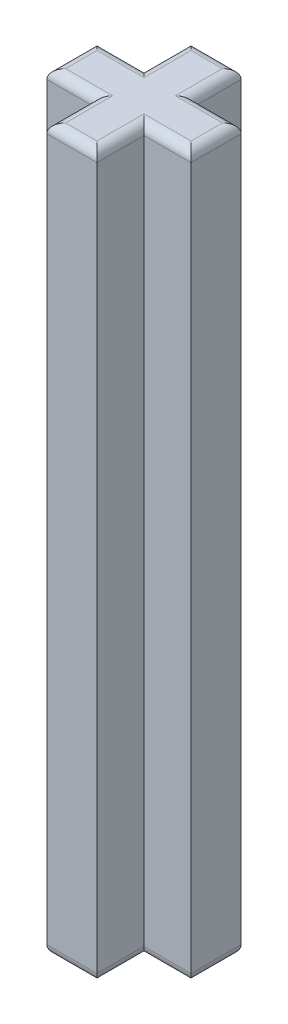
SolidWorks part; units mm, degrees
ref_plane "Front Plane" through (0, 0, 0) normal (0, 0, 1) x (1, 0, 0)
ref_plane "Top Plane" through (0, 0, 0) normal (0, 1, 0) x (1, 0, 0)
ref_plane "Right Plane" through (0, 0, 0) normal (1, 0, 0) x (0, 0, -1)
sketch "Sketch1" plane through (0, 0, 0) normal (0, 1, 0) x (1, 0, 0)
  line L0 (0.8, 0.8) -> (2.3, 0.8)
  line L1 (-2.3, -0.8) -> (-0.8, -0.8)
  line L2 (-2.3, -0.8) -> (-2.3, 0.8)
  line L3 (-2.3, 0.8) -> (-0.8, 0.8)
  line L4 (2.3, -0.8) -> (2.3, 0.8)
  line L5 (-2.3, -0.8) -> (2.3, 0.8) construction
  line L6 (-2.3, 0.8) -> (2.3, -0.8) construction
  line L7 (-0.8, -2.3) -> (0.8, -2.3)
  line L8 (-0.8, -2.3) -> (-0.8, -0.8)
  line L9 (-0.8, 2.3) -> (0.8, 2.3)
  line L10 (0.8, -2.3) -> (0.8, -0.8)
  line L11 (-0.8, -2.3) -> (0.8, 2.3) construction
  line L12 (-0.8, 2.3) -> (0.8, -2.3) construction
  line L13 (0.8, 0.8) -> (0.8, 2.3)
  line L14 (0.8, -0.8) -> (2.3, -0.8)
  line L15 (-0.8, 0.8) -> (-0.8, 2.3)
  point P0 (0, 0)
  point P6 (0, 0)
  dimension "D1" = 1.6
  dimension "D2" = 1.6
  dimension "D3" = 4.6
  dimension "D4" = 4.6
extrude "Boss-Extrude1" add sketch "Sketch1" along normal blind 23
fillet "Fillet1" radius 0.3 24 edges at (1.55, 0, -0.8) (0.8, 0, -1.55) (0, 0, -2.3) (-0.8, 0, -1.55) (-1.55, 0, -0.8) (-2.3, 0, 0) (-1.55, 0, 0.8) (-0.8, 0, 1.55) (0, 0, 2.3) (0.8, 0, 1.55) (1.55, 0, 0.8) (2.3, 0, 0) (1.55, 23, 0.8) (0.8, 23, 1.55) (0, 23, 2.3) (-0.8, 23, 1.55) (-1.55, 23, 0.8) (-2.3, 23, 0) (-1.55, 23, -0.8) (-0.8, 23, -1.55) (0, 23, -2.3) (0.8, 23, -1.55) (1.55, 23, -0.8) (2.3, 23, 0)
